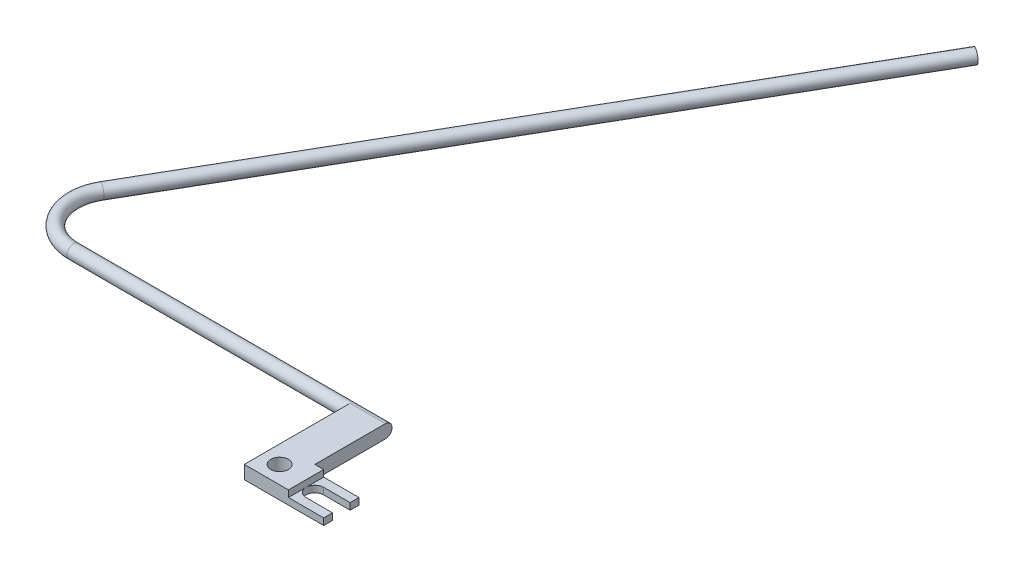
SolidWorks part; units mm, degrees
ref_plane "Front Plane" through (0, 0, 0) normal (0, 0, 1) x (1, 0, 0)
ref_plane "Top Plane" through (0, 0, 0) normal (0, 1, 0) x (1, 0, 0)
ref_plane "Right Plane" through (0, 0, 0) normal (1, 0, 0) x (0, 0, -1)
sketch "Sketch1" plane through (0, 0, 0) normal (0, 1, 0) x (1, 0, 0)
  line L0 (0, 0) -> (0, 20)
  line L1 (0, 20) -> (-8, 20)
  line L2 (-8, 20) -> (-8, -8)
  line L3 (-8, -8) -> (10, -8)
  line L4 (10, -8) -> (10, -6)
  line L5 (10, 0) -> (0, 0)
  line L6 (0, 0) -> (-8, -8) construction
  line L8 (4, -2) -> (10, -2)
  line L9 (4, -6) -> (10, -6)
  line L10 (10, -2) -> (10, 0)
  circle A0 centre (-4, -4) radius 2
  arc A1 (4, -2) -> (4, -6) centre (4, -4) ccw
  dimension "D6" = 4
  dimension "D8" = 4
  dimension "D1" = 10
  dimension "D2" = 8
  dimension "D4" = 28
  dimension "D5" = 8
extrude "Boss-Extrude1" add sketch "Sketch1" along normal blind 3
ref_plane "Plane1" through (0, 1.5, 0) normal (0, 1, 0) x (1, 0, 0)
sketch "Sketch2" plane through (0, 1.5, 0) normal (0, 1, 0) x (1, 0, 0)
  line L0 (-8, 20) -> (-8, 16) construction
  line L1 (-8, 20) -> (-8, -8) construction
  line L2 (10, -2) -> (6, -2) construction
  line L3 (4, -2) -> (10, -2) construction
  line L4 (6, -2) -> (6, 205.5036) construction
  line L5 (-8, 16) -> (-70.6795, 16)
  line L6 (-79.3397, 31) -> (-6.8397, 156.5737)
  arc A0 (-70.6795, 16) -> (-79.3397, 31) centre (-70.6795, 26) cw
  point P15 (-88, 16)
  dimension "D5" = 10
  dimension "D1" = 4
  dimension "D2" = 4
  dimension "D3" = 80
  dimension "D4" = 60
  dimension "D6" = 145
sketch "Sketch3" plane through (-8, 0, 0) normal (-1, 0, 0) x (0, 0, 1)
  line L0 (2, 1.5) -> (-205.5036, 1.5) construction
  circle A0 centre (-15.9964, 1.5) radius 1.5
sweep "Sweep1" add profiles "Sketch3" path "Sketch2"
sketch "Sketch4" plane through (0, 0, 0) normal (0, 0, -1) x (-1, 0, 0)
  line L1 (-10, 3) -> (-2, 3)
  line L2 (-10, 3) -> (-10, 1.5)
  line L3 (-10, 1.5) -> (-2, 1.5)
  line L4 (-2, 3) -> (-2, 1.5)
  dimension "D1" = 8
  dimension "D2" = 1.5
extrude "Cut-Extrude1" cut sketch "Sketch4" against normal blind 10
sketch "Sketch5" plane through (-8, 0, 0) normal (-1, 0, 0) x (0, 0, 1)
  line L1 (-15.9964, 3) -> (-20, 3)
  line L2 (-20, 3) -> (-20, 0)
  line L3 (-20, 0) -> (-15.9964, 0)
  arc A1 (-15.9964, 3) -> (-15.9964, 0) centre (-15.9964, 1.5) ccw
extrude "Cut-Extrude2" cut sketch "Sketch5" against normal blind 10
